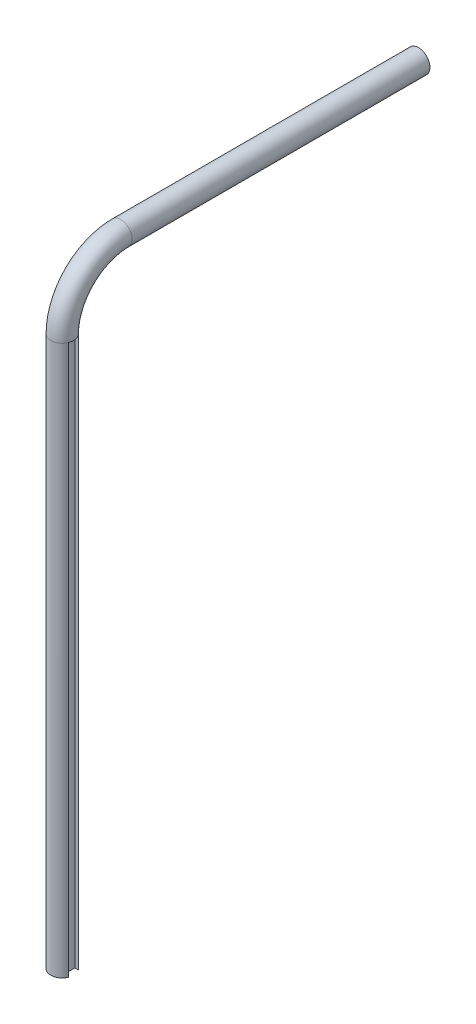
SolidWorks part; units mm, degrees
material "Cast Carbon Steel"
ref_plane "Front Plane" through (0, 0, 0) normal (0, 0, 1) x (1, 0, 0)
ref_plane "Top Plane" through (0, 0, 0) normal (0, 1, 0) x (1, 0, 0)
ref_plane "Right Plane" through (0, 0, 0) normal (1, 0, 0) x (0, 0, -1)
sketch "Sketch2" plane through (0, 0, 0) normal (1, 0, 0) x (0, 0, -1)
  arc A0 (-64.8338, 0) -> (0, 64.8338) centre (0, 0) cw
sketch "Sketch3" plane through (0, 0, 0) normal (0, 1, 0) x (1, 0, 0)
  circle A0 centre (0, -64.8338) radius 12.7
  circle A1 centre (0, -64.8338) radius 4.7625
  dimension "D1" = 25.4
  dimension "D2" = 7.9375
sweep "Sweep1" add profiles "Sketch3" path "Sketch2"
ref_plane "Plane1" through (0, 0, 0) normal (0, -1, 0) x (-1, 0, 0)
ref_plane "Plane2" through (0, 0, 0) normal (0, 0, -1) x (-1, 0, 0)
sketch "Sketch4" plane through (0, 0, 0) normal (0, -1, 0) x (-1, 0, 0)
  circle A0 centre (0, -64.8338) radius 12.7
  circle A1 centre (0, -64.8338) radius 4.7625
  dimension "D1" = 7.9375
  dimension "D2" = 25.4
extrude "Boss-Extrude3" add sketch "Sketch4" along normal blind 609.6
sketch "Sketch5" plane through (0, 0, 0) normal (0, 0, -1) x (-1, 0, 0)
  circle A0 centre (0, 64.8338) radius 12.7
  circle A1 centre (0, 64.8338) radius 4.7625
  dimension "D1" = 7.9375
  dimension "D2" = 25.4
extrude "Boss-Extrude4" add sketch "Sketch5" along normal blind 330.2
ref_plane "Plane3" through (-12.7, 0, 0) normal (-1, 0, 0) x (0, 0, 1)
ref_plane "Plane4" through (12.7, 0, 0) normal (1, 0, 0) x (0, 0, -1)
sketch "Sketch7" plane through (12.7, 0, 0) normal (1, 0, 0) x (0, 0, -1)
  line L0 (0, -55) -> (0, 55) construction
  line L1 (-69.85, 0) -> (-57.15, 0)
  line L2 (-69.85, 0) -> (-69.85, -609.6)
  line L3 (-69.85, -609.6) -> (-57.15, -609.6)
  line L4 (-57.15, 0) -> (-57.15, -609.6)
  line L5 (-52.1338, 0) -> (-77.5338, 0) construction
  point P9 (-63.5, -609.6)
  dimension "D1" = 12.7
  dimension "D2" = 609.6
  dimension "D3" = 57.15
  dimension "D4" = 63.5
extrude "Cut-Extrude2" cut sketch "Sketch7" against normal blind 6.35
